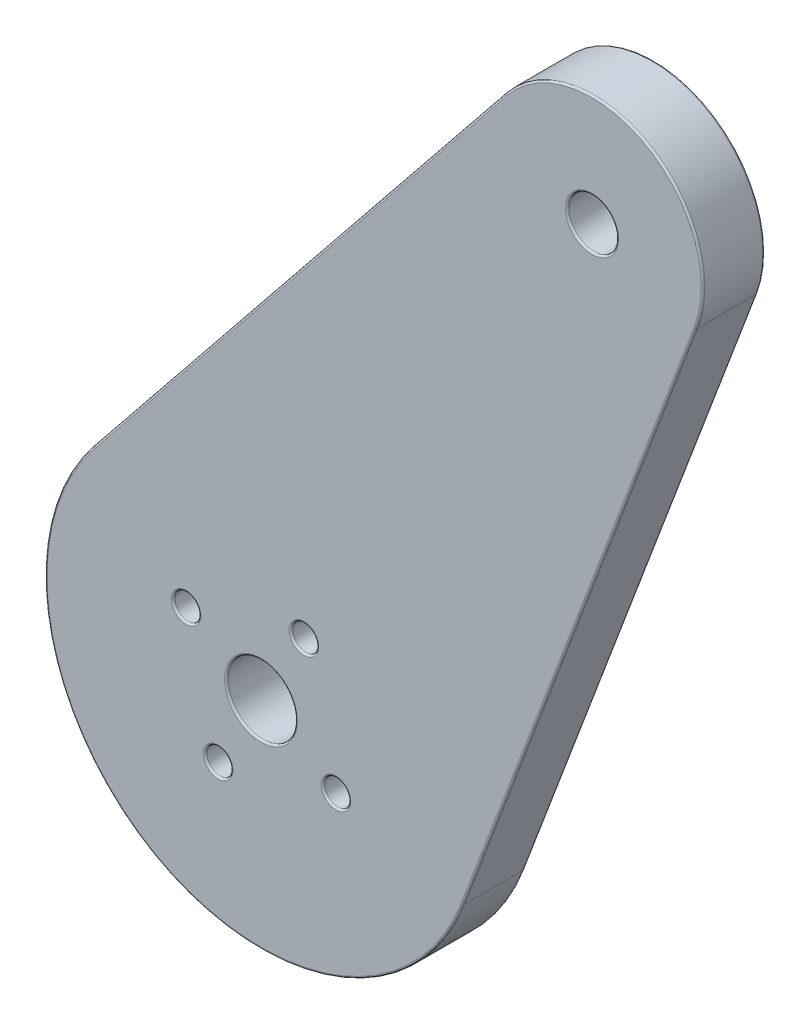
SolidWorks part; units mm, degrees
ref_plane "Front Plane" through (0, 0, 0) normal (0, 0, 1) x (1, 0, 0)
ref_plane "Top Plane" through (0, 0, 0) normal (0, 1, 0) x (1, 0, 0)
ref_plane "Right Plane" through (0, 0, 0) normal (1, 0, 0) x (0, 0, -1)
sketch "Sketch1" plane through (0, 0, 0) normal (0, 0, 1) x (1, 0, 0)
  line L0 (-20.22, 57.58) -> (6.6128, 104.4415) construction
  line L1 (-20.22, 57.58) -> (6.6128, 104.4415) construction
  line L2 (-33.8485, 68.5579) -> (-0.3961, 110.0873)
  line L3 (-3.8539, 51.3831) -> (15.0296, 101.2545)
  line L4 (-20.22, 57.58) -> (-35.4066, 66.2758) construction
  circle A0 centre (-20.22, 57.58) radius 17.5 construction
  circle A1 centre (-20.22, 57.58) radius 17.5 construction
  circle A2 centre (6.6128, 104.4415) radius 9 construction
  arc A3 (-3.8539, 51.3831) -> (-33.8485, 68.5579) centre (-20.22, 57.58) cw
  arc A4 (-0.3961, 110.0873) -> (15.0296, 101.2545) centre (6.6128, 104.4415) cw
  circle A5 centre (-20.22, 57.58) radius 2.8
  circle A6 centre (6.6128, 104.4415) radius 2
  circle A7 centre (-26.2946, 61.0583) radius 1.05
  circle A8 centre (-16.7417, 63.6546) radius 1.05
  circle A9 centre (-23.6983, 51.5054) radius 1.05
  circle A10 centre (-14.1454, 54.1017) radius 1.05
  dimension "D1" = 18
  dimension "D2" = 4
  dimension "D3" = 5.6
  dimension "D4" = 7
  dimension "D5" = 2.1
  dimension "D6" = 2.1
  dimension "D7" = 7
extrude "Boss-Extrude1" add sketch "Sketch1" against normal blind 5
fillet "Fillet1" radius 0.15 20 edges at (5.5878, 76.3188, -5) (11.0849, 112.2518, -5) (-17.1223, 89.3226, -5) (-28.9158, 42.3934, -5) (-17.42, 57.58, -5) (8.6128, 104.4415, -5) (-17.1223, 89.3226, 0) (11.0849, 112.2518, 0) (5.5878, 76.3188, 0) (-28.9158, 42.3934, 0) (-17.42, 57.58, 0) (8.6128, 104.4415, 0) (-25.2446, 61.0583, -5) (-15.6917, 63.6546, -5) (-24.7483, 51.5054, -5) (-15.1954, 54.1017, -5) (-25.2446, 61.0583, 0) (-15.6917, 63.6546, 0) (-24.7483, 51.5054, 0) (-15.1954, 54.1017, 0)
